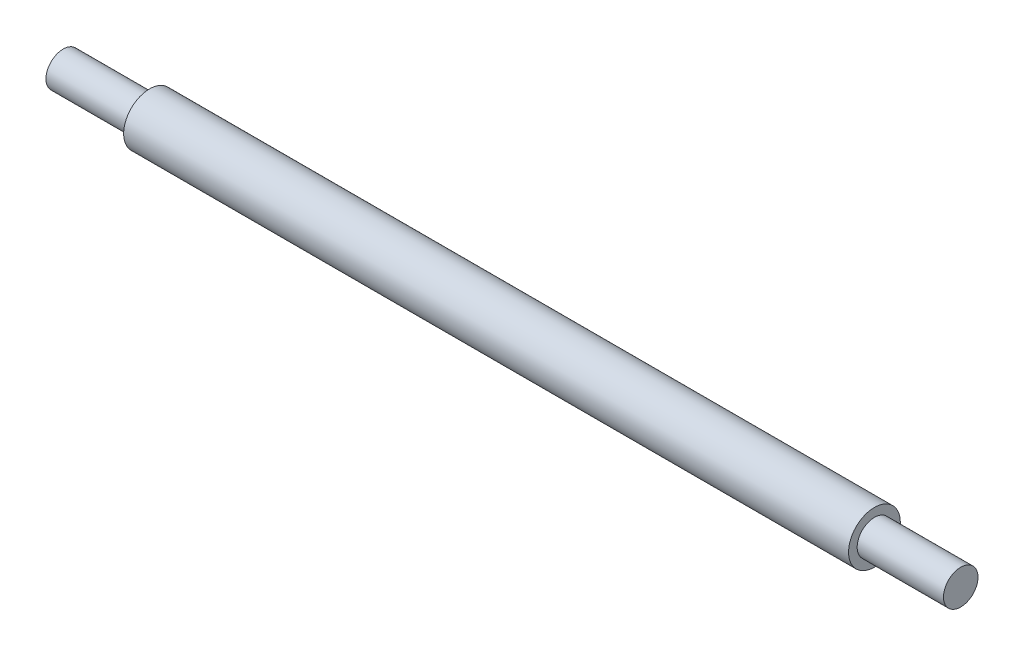
SolidWorks part; units mm, degrees
ref_plane "Front Plane" through (0, 0, 0) normal (0, 0, 1) x (1, 0, 0)
ref_plane "Top Plane" through (0, 0, 0) normal (0, 1, 0) x (1, 0, 0)
ref_plane "Right Plane" through (0, 0, 0) normal (1, 0, 0) x (0, 0, -1)
sketch "Sketch1" plane through (0, 0, 0) normal (1, 0, 0) x (0, 0, -1)
  circle A0 centre (0, 0) radius 2
  dimension "D1" = 4
extrude "Boss-Extrude1" add sketch "Sketch1" along normal blind 10
sketch "Sketch2" plane through (10, 0, 0) normal (1, 0, 0) x (0, 0, -1)
  circle A0 centre (0, 0) radius 3
  dimension "D1" = 6
extrude "Boss-Extrude2" add sketch "Sketch2" along normal blind 84
sketch "Sketch3" plane through (94, 0, 0) normal (1, 0, 0) x (0, 0, -1)
  circle A0 centre (0, 0) radius 2
  dimension "D1" = 4
extrude "Boss-Extrude3" add sketch "Sketch3" along normal blind 10
